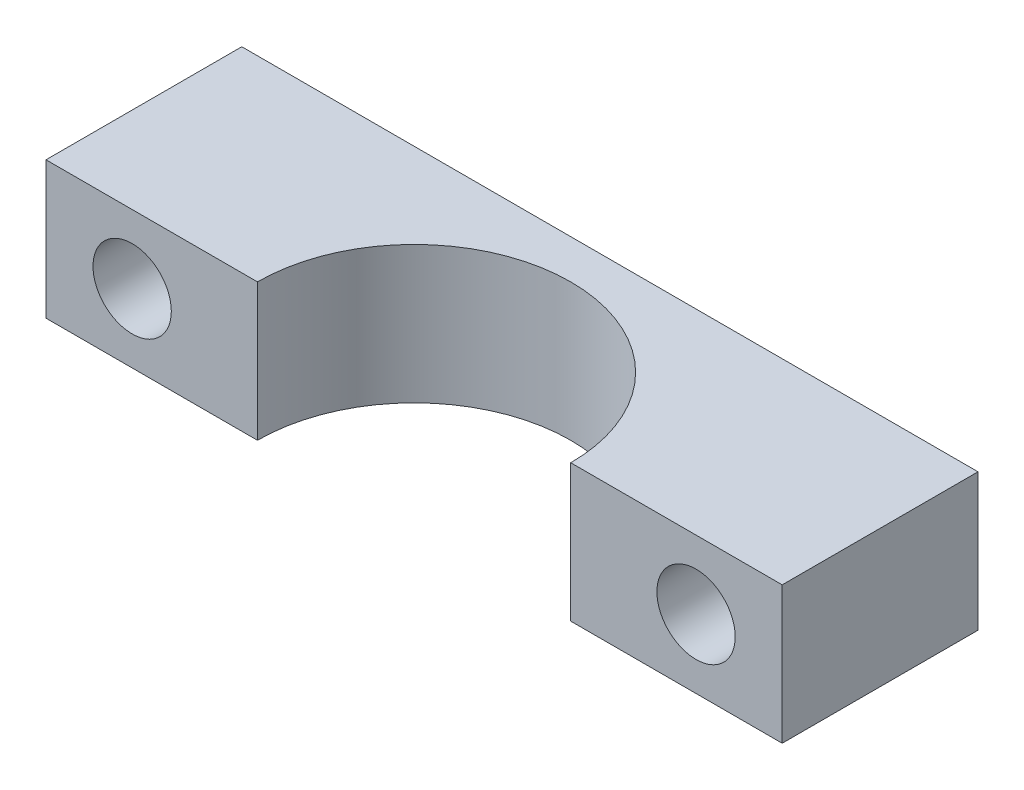
SolidWorks part; units mm, degrees
material "6061-T6 (SS)"
ref_plane "X-Y Datum" through (0, 0, 0) normal (0, 0, 1) x (1, 0, 0)
ref_plane "X-Z Datum" through (0, 0, 0) normal (0, 1, 0) x (1, 0, 0)
ref_plane "Y-Z Datum" through (0, 0, 0) normal (1, 0, 0) x (0, 0, -1)
sketch "Sketch1" plane through (0, 0, 0) normal (0, 1, 0) x (1, 0, 0)
  line L0 (-12.7, 0) -> (-29.845, 0)
  line L1 (-29.845, 0) -> (-29.845, 15.875)
  line L2 (-29.845, 15.875) -> (29.845, 15.875)
  line L3 (29.845, 15.875) -> (29.845, 0)
  line L4 (29.845, 0) -> (12.7, 0)
  line L10 (26.035, 0) -> (26.035, 15.875) construction
  line L11 (19.685, 0) -> (19.685, 15.875) construction
  line L12 (26.035, 7.9375) -> (19.685, 7.9375) construction
  arc A0 (-12.7, 0) -> (12.7, 0) centre (0, 0) cw
  point P16 (0, 0)
  point P17 (-17.7376, 0)
  point P18 (17.7376, 0)
  point P37 (22.86, 7.9375)
  dimension "D1" = 15.875
  dimension "D2" = 12.7
  dimension "D9" = 6.35
  dimension "D3" = 59.69
  dimension "D6" = 22.86
extrude "Boss-Extrude1" add sketch "Sketch1" along normal mid plane 11.1252
sketch "Sketch2" plane through (0, 0, 0) normal (0, 0, 1) x (1, 0, 0)
  line L0 (-22.86, 0) -> (22.86, 0) construction
  circle A0 centre (-22.86, 0) radius 3.175
  circle A1 centre (22.86, 0) radius 3.175
  point P4 (0, 0)
  dimension "D1" = 6.35
  dimension "D2" = 22.86
extrude "Cut-Extrude1" cut sketch "Sketch2" against normal through all
fillet "Fillet1" [suppressed] radius 3.81
fillet "Fillet2" [suppressed] radius 0.254
